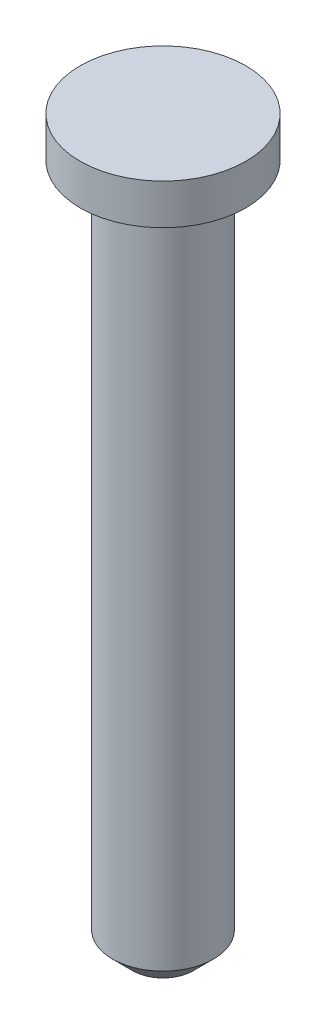
SolidWorks part; units mm, degrees
material "acero"
ref_plane "Alzado" through (0, 0, 0) normal (0, 0, 1) x (1, 0, 0)
ref_plane "Planta" through (0, 0, 0) normal (0, 1, 0) x (1, 0, 0)
ref_plane "Vista lateral" through (0, 0, 0) normal (1, 0, 0) x (0, 0, -1)
sketch "Croquis1" plane through (0, 0, 0) normal (0, 0, 1) x (1, 0, 0)
  line L0 (0, 0) -> (0, -60.9498) construction
  line L1 (0, 0) -> (2.05, 0)
  line L2 (2.05, 0) -> (2.05, -1)
  line L3 (2.05, -1) -> (1.25, -1)
  line L4 (1.25, -1) -> (1.25, -18)
  line L5 (1.25, -18) -> (0, -18)
  line L6 (0, -18) -> (0, 0)
  dimension "D1" = 18
  dimension "D2" = 1
  dimension "D3" = 4.1
  dimension "D4" = 2.5
revolve "Revolución1" add sketch "Croquis1" angle 360 about L0
chamfer "Chaflán1" distance 0.5 angle 45 1 edges at (0, -18, 1.25)
